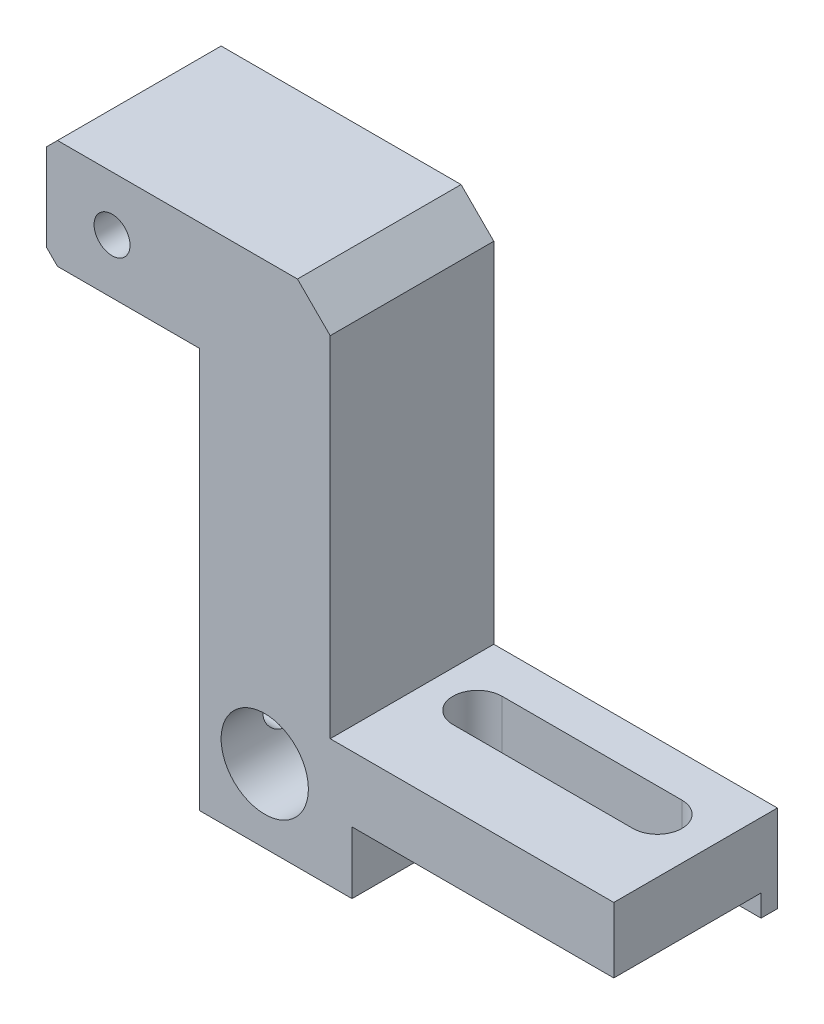
SolidWorks part; units mm, degrees
ref_plane "Front Plane" through (0, 0, 0) normal (0, 0, 1) x (1, 0, 0)
ref_plane "Top Plane" through (0, 0, 0) normal (0, 1, 0) x (1, 0, 0)
ref_plane "Right Plane" through (0, 0, 0) normal (1, 0, 0) x (0, 0, -1)
sketch "Sketch1" plane through (0, 0, 0) normal (0, 0, 1) x (1, 0, 0)
  line L0 (-19.7143, 7.0918) -> (6.2857, 7.0918)
  line L1 (6.2857, 7.0918) -> (6.2857, -27.9082)
  line L2 (6.2857, -27.9082) -> (32.2857, -27.9082)
  line L3 (32.2857, -27.9082) -> (32.2857, -33.9082)
  line L4 (32.2857, -33.9082) -> (8.2857, -33.9082)
  line L5 (8.2857, -33.9082) -> (8.2857, -39.6082)
  line L6 (8.2857, -39.6082) -> (-5.7143, -39.6082)
  line L7 (-5.7143, -39.6082) -> (-5.7143, -2.9082)
  line L8 (-5.7143, -2.9082) -> (-19.7143, -2.9082)
  line L9 (-19.7143, -2.9082) -> (-19.7143, 7.0918)
  circle A0 centre (0.2857, -32.9082) radius 4
  dimension "D11" = 8
  dimension "D1" = 10
  dimension "D2" = 14
  dimension "D3" = 26
  dimension "D4" = 35
  dimension "D5" = 6
  dimension "D6" = 24
  dimension "D7" = 5.7
  dimension "D8" = 26
  dimension "D9" = 6.7
  dimension "D10" = 6
extrude "Boss-Extrude1" add sketch "Sketch1" along normal blind 15
sketch "Sketch2" plane through (0, -33.9082, 0) normal (0, -1, 0) x (1, 0, 0)
  line L1 (32.2857, 0) -> (10.2857, 0)
  line L2 (32.2857, 0) -> (32.2857, 1.5)
  line L3 (32.2857, 1.5) -> (10.2857, 1.5)
  line L4 (10.2857, 0) -> (10.2857, 1.5)
  dimension "D1" = 1.5
  dimension "D2" = 22
extrude "Boss-Extrude2" add sketch "Sketch2" along normal blind 2
sketch "Sketch3" plane through (0, -27.9082, 0) normal (0, 1, 0) x (1, 0, 0)
  line L1 (10.7857, -3.75) -> (27.2857, -3.75)
  line L3 (10.7857, -8.25) -> (27.2857, -8.25)
  arc A0 (27.2857, -8.25) -> (27.2857, -3.75) centre (27.2857, -6) ccw
  arc A1 (10.7857, -3.75) -> (10.7857, -8.25) centre (10.7857, -6) ccw
  dimension "D2" = 16.5
  dimension "D4" = 4.5
extrude "Cut-Extrude1" cut sketch "Sketch3" against normal through all
hole_wizard "M4x0.7 Tapped Hole1" positions "Sketch4" profile "Sketch5" tap size "M4x0.7" standard "ANSI Metric"
sketch "Sketch4" plane through (-5.7143, 0, 0) normal (-1, 0, 0) x (0, 0, 1)
  line L0 (15, -2.9082) -> (15, -39.6082) construction
  line L2 (15, -39.6082) -> (0, -39.6082) construction
  point P0 (9.5, -32.9082)
  point P9 (11.6872, -39.6082)
  point P16 (9.5, -32.9691)
  point P17 (0, 0)
  dimension "D1" = 5.5
  dimension "D2" = 6.7
sketch "Sketch5" plane through (-5.7143, -32.9082, 9.5) normal (0, 1, 0) x (0, 0, 1)
  line L0 (0, 0) -> (0, 2)
  line L1 (0, 2) -> (1.65, 2)
  line L2 (1.65, 2) -> (1.65, 0)
  line L5 (1.65, 0) -> (0, 0)
  line L11 (0, -6.35) -> (0, 107.95) construction
  dimension "Thru Tap Drill Dia." = 3.3
  dimension "Thru Tap Drill Depth" = 2
cosmetic thread "Hole Thread1" parameters "D2"=4
hole_wizard "M4x0.7 Tapped Hole2" positions "Sketch6" profile "Sketch7" tap size "M4x0.7" standard "ANSI Metric"
sketch "Sketch6" plane through (0, 0, 15) normal (0, 0, 1) x (1, 0, 0)
  line L0 (-19.7143, -2.9082) -> (-5.7143, -2.9082) construction
  line L1 (-19.7143, 7.0918) -> (-19.7143, -2.9082) construction
  point P0 (-13.7143, 2.0918)
  point P3 (0, 0)
  dimension "D1" = 5
  dimension "D2" = 6
sketch "Sketch7" plane through (-13.7143, 2.0918, 15) normal (1, 0, 0) x (0, -1, 0)
  line L0 (0, 0) -> (0, 8.9914)
  line L1 (0, 8.9914) -> (1.65, 8)
  line L2 (1.65, 8) -> (1.65, 0)
  line L5 (1.65, 0) -> (0, 0)
  line L10 (0, 8.9914) -> (-1.65, 8) construction
  line L11 (0, -6.35) -> (0, 107.95) construction
  dimension "Tap Drill Dia." = 3.3
  dimension "Tap Drill Depth" = 8
  dimension "Drill Angle" = 118
cosmetic thread "Hole Thread2" parameters "D1"=8, "D2"=4
chamfer "Chamfer1" distance 1 angle 45 2 edges at (-19.7143, -2.9082, 7.5) (-19.7143, 7.0918, 7.5)
chamfer "Chamfer2" distance 3 angle 45 1 edges at (6.2857, 7.0918, 7.5)
